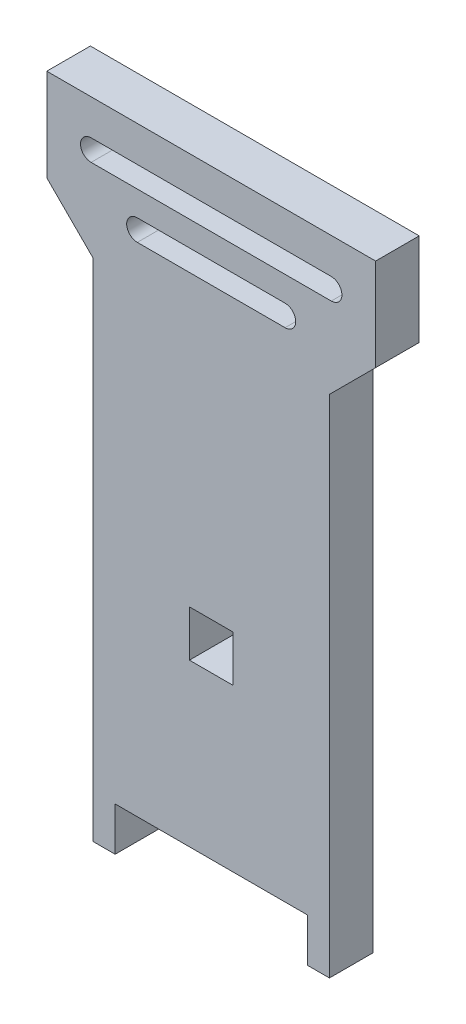
SolidWorks part; units mm, degrees
material "Acrylic (Medium-high impact)"
ref_plane "Front Plane" through (0, 0, 0) normal (0, 0, 1) x (1, 0, 0)
ref_plane "Top Plane" through (0, 0, 0) normal (0, 1, 0) x (1, 0, 0)
ref_plane "Right Plane" through (0, 0, 0) normal (1, 0, 0) x (0, 0, -1)
sketch "Sketch1" plane through (0, 0, 0) normal (0, 0, 1) x (1, 0, 0)
  line L0 (16.256, 0) -> (13.208, 0)
  line L1 (13.208, 0) -> (13.208, 5.9944)
  line L2 (13.208, 5.9944) -> (-13.208, 5.9944)
  line L3 (-16.256, 0) -> (-13.208, 0)
  line L4 (-13.208, 0) -> (-13.208, 5.9944)
  line L5 (-22.606, 75.8444) -> (-22.606, 88.5444)
  line L6 (-2.9972, 34.5694) -> (-2.9972, 28.2194)
  line L7 (-10.16, 77.3049) -> (10.16, 77.3049)
  line L8 (-2.9972, 34.5694) -> (2.9972, 34.5694)
  line L9 (2.9972, 34.5694) -> (2.9972, 28.2194)
  line L10 (2.9972, 28.2194) -> (-2.9972, 28.2194)
  line L11 (-16.51, 83.6549) -> (16.51, 83.6549)
  line L12 (16.256, 0) -> (16.256, 69.4944)
  line L13 (-16.51, 80.7339) -> (16.51, 80.7339)
  line L14 (0, 0) -> (0, 20.4016) construction
  line L15 (-10.16, 74.3839) -> (10.16, 74.3839)
  line L16 (16.256, 69.4944) -> (22.606, 75.8444)
  line L17 (22.606, 75.8444) -> (22.606, 88.5444)
  line L18 (-16.256, 69.4944) -> (-22.606, 75.8444)
  line L19 (-16.256, 0) -> (-16.256, 69.4944)
  line L25 (22.606, 88.5444) -> (-22.606, 88.5444)
  arc A0 (10.16, 74.3839) -> (10.16, 77.3049) centre (10.16, 75.8444) ccw
  arc A1 (16.51, 80.7339) -> (16.51, 83.6549) centre (16.51, 82.1944) ccw
  arc A2 (-16.51, 80.7339) -> (-16.51, 83.6549) centre (-16.51, 82.1944) cw
  arc A3 (-10.16, 74.3839) -> (-10.16, 77.3049) centre (-10.16, 75.8444) cw
  point P8 (0, 5.9944)
  point P13 (0, 28.2194)
  point P14 (0, 34.5694)
  point P15 (0, 83.6549)
  point P29 (0, 80.7339)
  point P31 (0, 77.3049)
  point P33 (0, 74.3839)
  point P42 (0, 88.5444)
  dimension "D6" = 28.575
  dimension "D12" = 1.4605
  dimension "D13" = 6.35
  dimension "D10" = 1.4605
  dimension "D15" = 135
  dimension "D2" = 16.256
  dimension "D3" = 3.048
  dimension "D4" = 2.9972
  dimension "D5" = 6.35
  dimension "D7" = 5.9944
  dimension "D8" = 82.55
  dimension "D9" = 16.51
  dimension "D11" = 6.35
  dimension "D14" = 6.35
  dimension "D16" = 6.35
  dimension "D17" = 12.7
extrude "Boss-Extrude1" add sketch "Sketch1" along normal blind 5.9944
